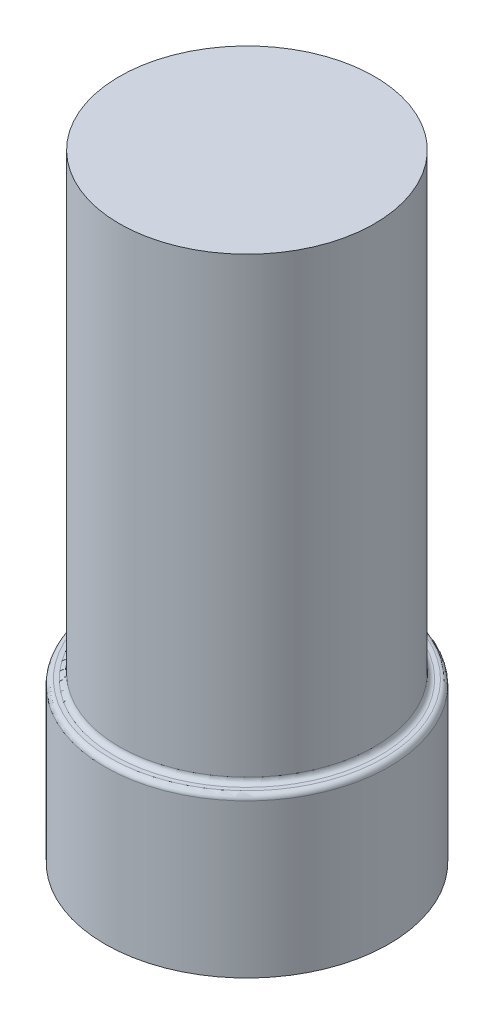
SolidWorks part; units mm, degrees
ref_plane "Front Plane" through (0, 0, 0) normal (0, 0, 1) x (1, 0, 0)
ref_plane "Top Plane" through (0, 0, 0) normal (0, 1, 0) x (1, 0, 0)
ref_plane "Right Plane" through (0, 0, 0) normal (1, 0, 0) x (0, 0, -1)
sketch "Sketch1" plane through (0, 0, 0) normal (0, 1, 0) x (1, 0, 0)
  circle A0 centre (0, 0) radius 13.75
  dimension "D1" = 27.5
extrude "Boss-Extrude1" add sketch "Sketch1" along normal blind 15.35
sketch "Sketch2" plane through (0, 15.35, 0) normal (0, 1, 0) x (1, 0, 0)
  circle A0 centre (0, 0) radius 12.35
  dimension "D1" = 24.7
extrude "Boss-Extrude2" add sketch "Sketch2" along normal offset from surface (44.35 mm away) 59.7 up to plane "Top Plane"
fillet "Fillet1" radius 0.5 2 edges at (0, 15.35, 12.35) (0, 15.35, 13.75)
sketch "Sketch3" plane through (0, 0, 0) normal (0, -1, 0) x (1, 0, 0)
  circle A0 centre (0, 0) radius 2.8
  dimension "D1" = 5.6
extrude "Cut-Extrude1" cut sketch "Sketch3" against normal blind 3
sketch "Sketch4" plane through (0, 3, 0) normal (0, -1, 0) x (1, 0, 0)
  circle A0 centre (0, 0) radius 0.5
  dimension "D1" = 1
extrude "Boss-Extrude3" add sketch "Sketch4" along normal blind 2.5
chamfer "Chamfer1" distance 0.5 angle 45 1 edges at (0, 0.5, -0.5)
